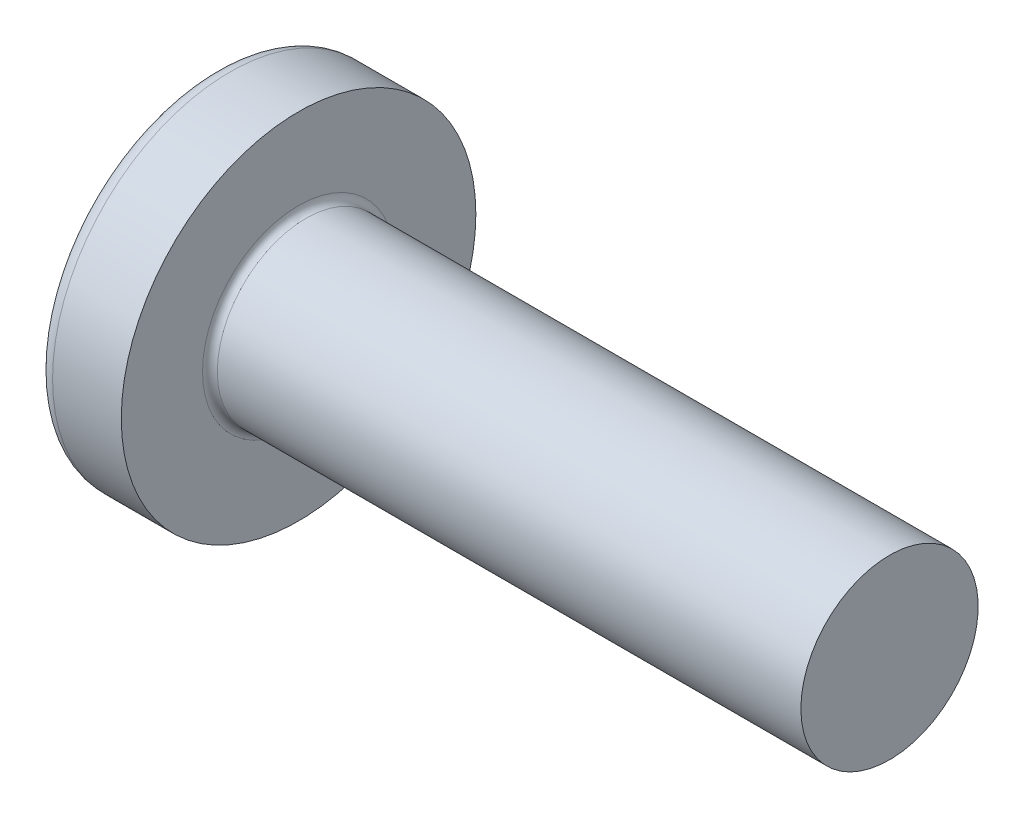
SolidWorks part; units mm, degrees
ref_plane "Plane1" through (0, 0, 0) normal (0, 0, 1) x (1, 0, 0)
ref_plane "Plane2" through (0, 0, 0) normal (0, 1, 0) x (1, 0, 0)
ref_plane "Plane3" through (0, 0, 0) normal (1, 0, 0) x (0, 0, -1)
sketch "BodySke" plane through (0, 0, 0) normal (0, 0, 1) x (1, 0, 0)
  line L0 (4.6, 3) -> (4.6, 6)
  line L1 (5.1, 6.35) -> (5.1, -3.175) construction
  line L2 (-25.4, 0) -> (127, 0) construction
  line L3 (24.6, 0) -> (0, 0)
  line L4 (4.6, 3) -> (24.6, 3)
  line L5 (24.6, 3) -> (24.6, 0)
  line L6 (2.2747, 6) -> (4.6, 6)
  line L8 (4.6, 6.35) -> (4.6, -3.175) construction
  arc A0 (1.8337, 5.7717) -> (0, 0) centre (10, 0) ccw
  arc A2 (1.8337, 5.7717) -> (2.2747, 6) centre (2.2747, 5.46) cw
  dimension "Length" = 20
  dimension "Thread_nom" = 20
revolve "Base-Revolve" add sketch "BodySke"
cosmetic thread "ThreadCosmetic" [suppressed]
fillet "Fillet1" radius 0.25 1 edges at (4.6, 0, 3)
sketch "Sketch3" plane through (0, 0, 0) normal (1, 0, 0) x (0, 0, -1)
  line L0 (0.71, -3.35) -> (-0.71, -3.35)
  line L1 (0.71, -3.35) -> (0.71, 3.35)
  line L2 (-0.71, 3.35) -> (0.71, 3.35)
  line L3 (-0.71, 3.35) -> (-0.71, -3.35)
  dimension "D1" = 1.4
  dimension "D2" = 0.37
ref_plane "Plane4" through (3.46, 0, 0) normal (1, 0, 0) x (0, 0, -1)
sketch "Sketch4" plane through (3.46, 0, 0) normal (1, 0, 0) x (0, 0, -1)
  line L0 (0.71, -1.6249) -> (-0.71, -1.6249)
  line L1 (0.71, -1.6249) -> (0.71, 1.6249)
  line L2 (-0.71, 1.6249) -> (0.71, 1.6249)
  line L3 (-0.71, 1.6249) -> (-0.71, -1.6249)
  dimension "D1" = 0.74
  dimension "D2" = 1.055
  dimension "D3" = 0.37
  dimension "D4" = 0.5275
loft "Recess" cut profiles "Sketch3", "Sketch4"
pattern_circular "RecPat" count 2 every 90 about axis through (0, 0, 0) along (1, 0, 0) of "Recess"
sketch "RecCorSke" plane through (0, 0, 0) normal (0, 0, 1) x (1, 0, 0)
  line L0 (-3.175, 0) -> (15.875, 0) construction
  line L1 (-25.4, 0) -> (127, 0) construction
  line L2 (0, 0) -> (0, 1.5224)
  line L3 (0, 1.5224) -> (3.46, 1.2805)
  line L4 (3.46, 1.2805) -> (3.8761, 0)
  line L5 (3.8761, 0) -> (0, 0)
  dimension "Depth" = 1.75
  dimension "Draft_angle" = 4
  dimension "Bottom_angle" = 18
revolve "RecessCore" cut sketch "RecCorSke" angle 360 about L0
sketch "ThdSchSke" plane through (0, 0, 0) normal (0, 0, 1) x (1, 0, 0)
  line L0 (6.6, -2.4455) -> (6.2117, -3)
  line L1 (6.6, -2.4455) -> (6.9883, -3)
  line L2 (6.9883, -3) -> (6.9883, -3.75)
  line L3 (-3.175, 0) -> (5.1513, 0) construction
  line L5 (6.9883, -3.75) -> (6.2117, -3.75)
  line L6 (6.2117, -3.75) -> (6.2117, -3)
  dimension "SideAngle" = 55
  dimension "VeeAngle" = 70
  dimension "Thread_minor" = 2.439
  dimension "Overcut" = 3.75
  dimension "Diameter" = 3
  dimension "Start" = 3.4
revolve "ThreadSchematic" [suppressed] cut sketch "ThdSchSke" angle 360 about L3
pattern_linear "ThdSchPat" [suppressed]
equation "\"D1@Sketch3\" = \"Cross_dia@Sketch3\" / 2"
equation "\"D2@Sketch3\" = \"Cross_width@Sketch3\" / 2"
equation "\"Depth@RecCorSke\" = \"Cross_depth@Plane4\""
equation "\"D1@Sketch4\" = \"Cross_width@Sketch3\""
equation "\"D2@Sketch4\" = \"Cross_dia@Sketch3\" - 2.0 * \"Cross_depth@Plane4\" * tan(26.5  * 0.017453292)"
equation "\"D3@Sketch4\" = \"D1@Sketch4\" / 2"
equation "\"D4@Sketch4\" = \"D2@Sketch4\" / 2"
equation "\"Thread_length@ThreadCosmetic\" = ((sgn( (\"Length@BodySke\" - \"Advance@BodySke\" * 2.0 ) - \"Thread_nom@BodySke\" )-1)*( (\"Length@BodySke\" - \"Advance@BodySke\" * 2.0 ) - \"Thread_nom@BodySke\" ))/-2+ \"Thread_nom@BodySke\""
equation "\"Thread_minor@ThdSchSke\" = \"Thread_minor@ThreadCosmetic\""
equation "\"Diameter@ThdSchSke\" = \"Diameter@BodySke\""
equation "\"Overcut@ThdSchSke\" = \"Diameter@BodySke\" * 1.25"
equation "\"Start@ThdSchSke\" = \"Head_ht@BodySke\" + \"Length@BodySke\" - \"Thread_length@ThreadCosmetic\"  '---Non-countersunk---"
equation "\"Num_threads@ThdSchPat\" = int( \"Thread_length@ThreadCosmetic\" / \"Advance@BodySke\" + 0.999 )  + 1"
equation "\"Advance@ThdSchPat\" = \"Thread_length@ThreadCosmetic\" /  (\"Num_threads@ThdSchPat\" - 1) 'relax it"
